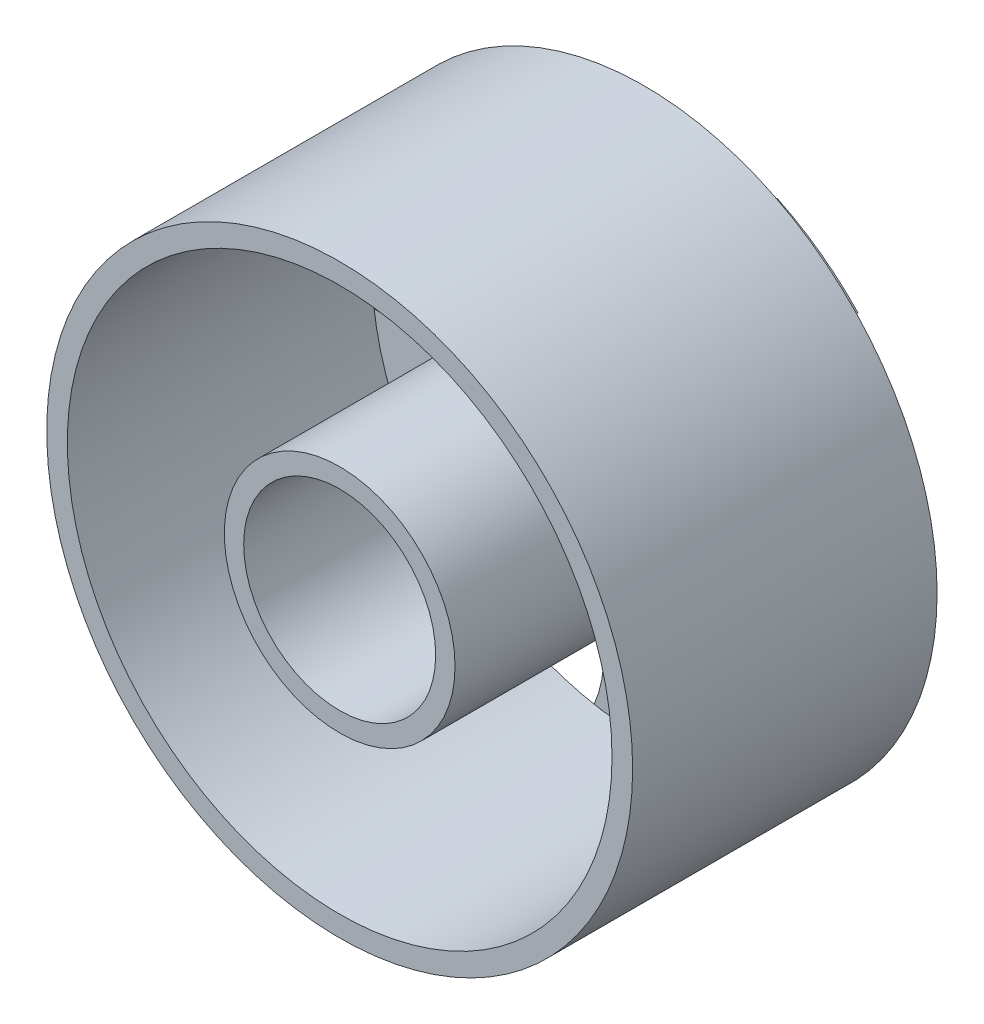
SolidWorks part; units mm, degrees
ref_plane "Front Plane" through (0, 0, 0) normal (0, 0, 1) x (1, 0, 0)
ref_plane "Top Plane" through (0, 0, 0) normal (0, 1, 0) x (1, 0, 0)
ref_plane "Right Plane" through (0, 0, 0) normal (1, 0, 0) x (0, 0, -1)
sketch "Sketch1" plane through (0, 0, 0) normal (0, 0, 1) x (1, 0, 0)
  circle A4 centre (0, 0) radius 13.931
  circle A5 centre (0, 0) radius 12.9511
  circle A6 centre (0, 0) radius 5.4853
  circle A7 centre (0, 0) radius 4.5651
extrude "Boss-Extrude1" add sketch "Sketch1" along normal blind 14.478 contours A4 A5 | A6 A7
sketch "Sketch2" plane through (0, 0, 0) normal (0, 0, -1) x (-1, 0, 0)
  circle A0 centre (0, 0) radius 12.9511
extrude "Boss-Extrude2" add sketch "Sketch2" along normal blind 0.762
sketch "Sketch4" plane through (0, 0, -0.762) normal (0, 0, -1) x (-1, 0, 0)
  circle A0 centre (0, 12.9511) radius 5.6991
  circle A1 centre (0, 0) radius 12.9511 construction
  circle A2 centre (0, 0) radius 12.9511 construction
extrude "Cut-Extrude2" cut sketch "Sketch4" against normal blind 0.762
pattern_circular "CirPattern2" count 5 over 360 about axis through (0, 0, 0) along (0, 0, 1) of "Cut-Extrude2"
sketch "Sketch6" plane through (0, 0, 0) normal (0, 0, 1) x (1, 0, 0)
  circle A0 centre (0, 0) radius 4.5651
extrude "Cut-Extrude3" cut sketch "Sketch6" against normal blind 0.762
